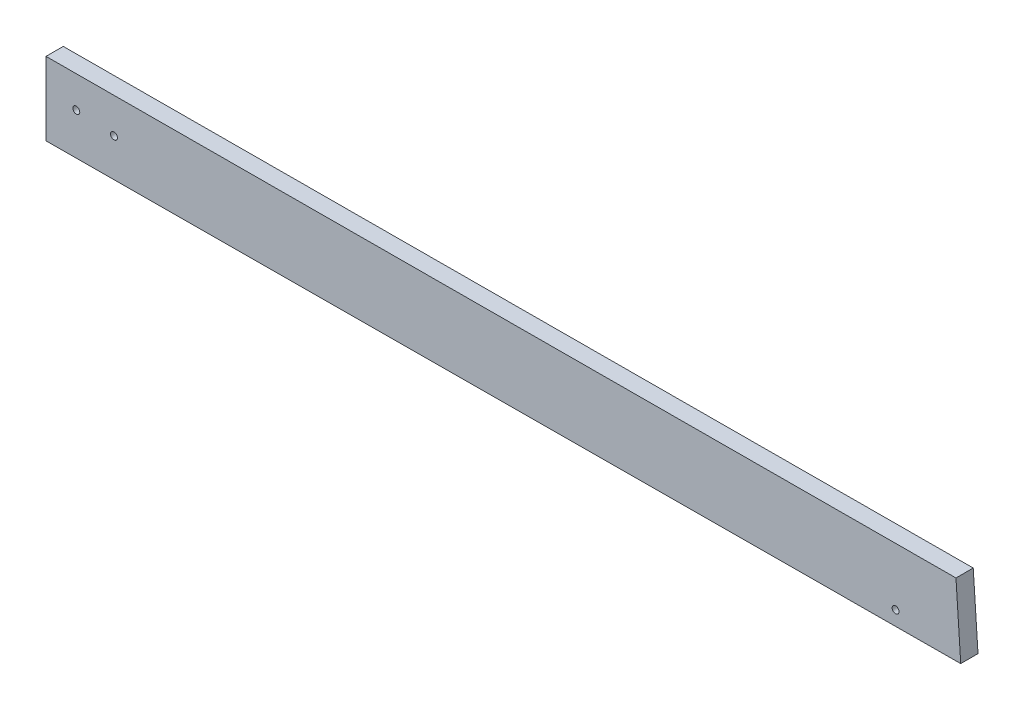
SolidWorks part; units mm, degrees
ref_plane "Front Plane" through (0, 0, 0) normal (0, 0, 1) x (1, 0, 0)
ref_plane "Top Plane" through (0, 0, 0) normal (0, 1, 0) x (1, 0, 0)
ref_plane "Right Plane" through (0, 0, 0) normal (1, 0, 0) x (0, 0, -1)
sketch "Sketch1" plane through (0, 0, 0) normal (0, 0, 1) x (1, 0, 0)
  line L0 (169.0002, 139.8587) -> (169.8769, 126.6509) construction
  line L1 (1.5875, 125.7946) -> (1.5875, 139.2577) construction
  line L2 (169.0002, 139.8587) -> (169.8769, 126.6509)
  line L3 (1.5875, 125.7946) -> (1.5875, 139.2577)
  line L4 (1.5875, 139.2577) -> (169.0002, 139.8587)
  line L5 (169.8769, 126.6509) -> (1.5875, 125.7946)
  circle A0 centre (7.1637, 133.4774) radius 0.635
  circle A1 centre (14.0875, 132.8424) radius 0.635
  circle A2 centre (157.8929, 129.2356) radius 0.635
  dimension "D1" = 1.27
  dimension "D2" = 1.27
  dimension "D3" = 1.27
extrude "Boss-Extrude1" add sketch "Sketch1" against normal blind 3.175 contours L5 L2 L4 L3 A2 A1 A0
